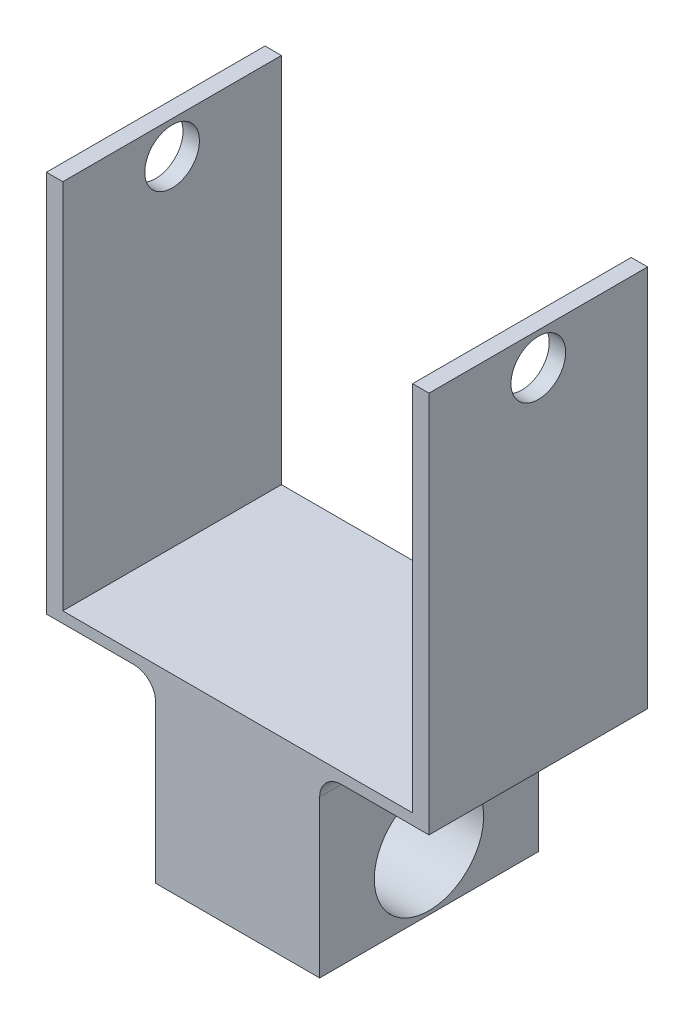
SolidWorks part; units mm, degrees
ref_plane "Front Plane" through (0, 0, 0) normal (0, 0, 1) x (1, 0, 0)
ref_plane "Top Plane" through (0, 0, 0) normal (0, 1, 0) x (1, 0, 0)
ref_plane "Right Plane" through (0, 0, 0) normal (1, 0, 0) x (0, 0, -1)
sketch "Sketch1" plane through (0, 0, 0) normal (0, 1, 0) x (1, 0, 0)
  line L1 (-17.5, 0) -> (17.5, 0)
  line L2 (-17.5, 0) -> (-17.5, 20)
  line L3 (-17.5, 20) -> (17.5, 20)
  line L4 (17.5, 0) -> (17.5, 20)
  point P4 (0, 0)
  dimension "D1" = 35
  dimension "D2" = 20
extrude "Boss-Extrude1" add sketch "Sketch1" along normal blind 40
sketch "Sketch2" plane through (0, 0, 0) normal (0, -1, 0) x (1, 0, 0)
  line L6 (0, 0) -> (0, -20) construction
  line L7 (17.5, -20) -> (-17.5, -20) construction
  line L9 (-7.5, -20) -> (7.5, -20)
  line L10 (-7.5, -20) -> (-7.5, 0)
  line L11 (-7.5, 0) -> (7.5, 0)
  line L12 (7.5, -20) -> (7.5, 0)
  line L13 (-7.5, -20) -> (7.5, 0) construction
  line L14 (-7.5, 0) -> (7.5, -20) construction
  point P4 (0, -10)
  dimension "D1" = 15
  dimension "D2" = 20
extrude "Boss-Extrude2" add sketch "Sketch2" along normal blind 16
sketch "Sketch3" plane through (-7.5, 0, 0) normal (-1, 0, 0) x (0, 0, 1)
  line L0 (-10, -16) -> (-10, -6) construction
  line L1 (0, -16) -> (-20, -16) construction
  circle A0 centre (-10, -6) radius 5
  dimension "D2" = 10
  dimension "D1" = 10
extrude "Cut-Extrude1" cut sketch "Sketch3" against normal through all
fillet "Fillet3" radius 3 2 edges at (7.5, -16, -10) (-7.5, -16, -10)
sketch "Sketch4" plane through (0, 0, 0) normal (0, 0, 1) x (1, 0, 0)
  line L0 (0, 40) -> (0, 0) construction
  line L1 (-17.5, 40) -> (17.5, 40) construction
  line L3 (-16, 40) -> (16, 40)
  line L4 (-16, 40) -> (-16, 6)
  line L5 (-16, 6) -> (16, 6)
  line L6 (16, 40) -> (16, 6)
  point P9 (0, 40)
  dimension "D1" = 32
  dimension "D2" = 34
extrude "Cut-Extrude2" cut sketch "Sketch4" against normal through all
sketch "Sketch5" plane through (-17.5, 0, 0) normal (-1, 0, 0) x (0, 0, 1)
  line L0 (-10, 40) -> (-10, 37) construction
  line L1 (-20, 40) -> (0, 40) construction
  circle A0 centre (-10, 37) radius 2.5
  dimension "D2" = 5
  dimension "D1" = 3
extrude "Cut-Extrude3" cut sketch "Sketch5" against normal through all
sketch "Sketch7" plane through (0, 0, -20) normal (0, 0, -1) x (-1, 0, 0)
  line L0 (-7.5, 0) -> (-7.5, 3.537) construction
  line L1 (0, 0) -> (0, 7.9214) construction
  line L2 (17.5, 5) -> (7.5, 5)
  line L3 (-17.5, 0) -> (-7.5, 0)
  line L4 (-17.5, 0) -> (-17.5, 5)
  line L5 (-17.5, 5) -> (-7.5, 5)
  line L6 (-7.5, 0) -> (-7.5, 5)
  line L7 (7.5, 0) -> (7.5, 5)
  line L8 (17.5, 0) -> (7.5, 0)
  line L9 (17.5, 0) -> (17.5, 5)
  dimension "D1" = 5
extrude "Cut-Extrude4" cut sketch "Sketch7" against normal through all
fillet "Fillet5" radius 2 2 edges at (-7.5, 5, -10) (7.5, 5, -10)
sketch "Sketch8" plane through (0, 0, 0) normal (1, 0, 0) x (0, 0, -1)
  line L0 (20, -13) -> (20, 3) construction
  line L1 (0, -16) -> (20, -16)
  line L2 (0, -16) -> (0, -11.3318)
  line L3 (0, -11.3318) -> (20, -11.3318)
  line L4 (20, -16) -> (20, -11.3318)
extrude "Cut-Extrude5" cut sketch "Sketch8" against normal through all both and the other way through all contours L4 L3 L2 L1
